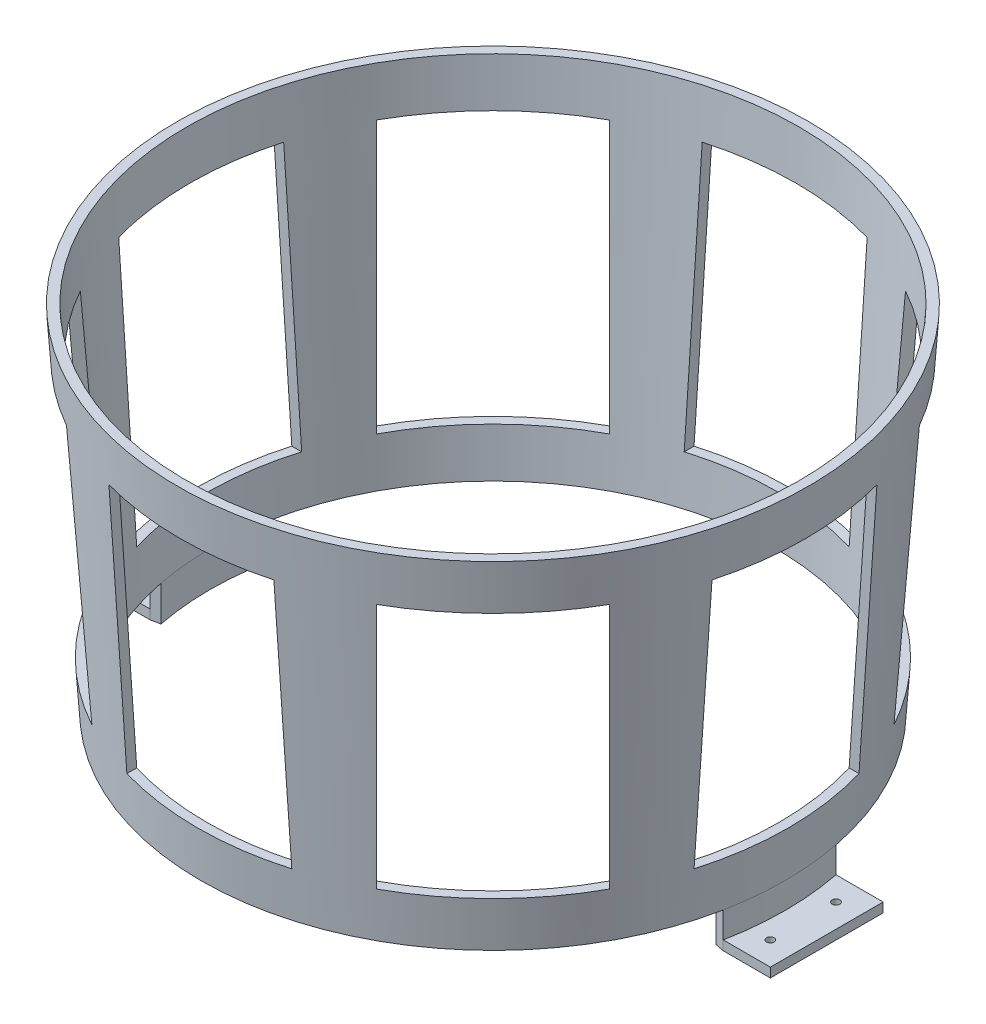
SolidWorks part; units mm, degrees
ref_plane "Front Plane" through (0, 0, 0) normal (0, 0, 1) x (1, 0, 0)
ref_plane "Top Plane" through (0, 0, 0) normal (0, 1, 0) x (1, 0, 0)
ref_plane "Right Plane" through (0, 0, 0) normal (1, 0, 0) x (0, 0, -1)
sketch "Sketch2" plane through (0, 0, 0) normal (0, 0, 1) x (1, 0, 0)
  line L1 (120, 0) -> (130, 150)
  line L2 (0, 0) -> (0, 173.8578) construction
  line L7 (120, 0) -> (124.0089, 0)
  line L8 (0, 0) -> (134.0323, 0) construction
  line L9 (130, 150) -> (134.0089, 150)
  line L10 (134.0089, 150) -> (124.0089, 0)
  dimension "D1" = 120
  dimension "D2" = 130
  dimension "D3" = 4
  dimension "D4" = 150
  dimension "D5" = 4
  dimension "D6" = 4.0089
revolve "Revolve1" add sketch "Sketch2" angle 360 about L2
sketch "Sketch4" [suppressed] plane through (0, 0, 0) normal (0, 0, 1) x (1, 0, 0)
  line L0 (0, 0) -> (0, 150) construction
  line L1 (-124.0089, 0) -> (124.0089, 0) construction
  line L2 (130, 150) -> (-130, 150) construction
  line L3 (110, 25) -> (110, 125)
  line L4 (-20, 25) -> (-50, 25)
  line L5 (-20, 25) -> (-20, 125)
  line L6 (-20, 125) -> (-50, 125)
  line L7 (-50, 25) -> (-50, 125)
  line L8 (-70, 25) -> (-110, 25)
  line L9 (-70, 25) -> (-70, 125)
  line L10 (-70, 125) -> (-110, 125)
  line L11 (-110, 25) -> (-110, 125)
  line L12 (70, 25) -> (70, 125)
  line L13 (70, 25) -> (110, 25)
  line L14 (20, 25) -> (50, 25)
  line L15 (20, 25) -> (20, 125)
  line L16 (50, 25) -> (50, 125)
  line L17 (20, 125) -> (50, 125)
  line L18 (70, 125) -> (110, 125)
  dimension "D1" = 40
  dimension "D2" = 30
  dimension "D3" = 20
  dimension "D4" = 20
  dimension "D5" = 25
  dimension "D6" = 25
  dimension "D7" = 25
  dimension "D8" = 25
ref_plane "Plane2" through (0, 0, 134) normal (0, 0, 1) x (1, 0, 0)
sketch "Sketch6" plane through (0, 0, 134) normal (0, 0, 1) x (1, 0, 0)
  line L0 (0, 0) -> (0, 150) construction
  line L1 (134.0089, 150) -> (-134.0089, 150) construction
  line L3 (-35, 130) -> (35, 130)
  line L4 (-35, 130) -> (-35, 20)
  line L5 (-35, 20) -> (35, 20)
  line L6 (35, 130) -> (35, 20)
  dimension "D1" = 70
  dimension "D2" = 20
  dimension "D3" = 20
extrude "Cut-Extrude2" cut sketch "Sketch6" against normal mid plane 40
sketch "Sketch7" plane through (0, 0, 0) normal (0, 1, 0) x (1, 0, 0)
  line L0 (-117.7443, 23.1577) -> (-121.6778, 23.9314)
  line L2 (-117.7443, -23.1577) -> (-121.6778, -23.9314)
  line L3 (117.7443, -23.1577) -> (121.6778, -23.9314)
  line L4 (117.7443, 23.1577) -> (121.6778, 23.9314)
  circle A0 centre (0, 0) radius 120 construction
  circle A1 centre (0, 0) radius 124.0089 construction
  arc A2 (117.7443, -23.1577) -> (117.7443, 23.1577) centre (0, 0) ccw
  arc A3 (121.6778, -23.9314) -> (121.6778, 23.9314) centre (0, 0) ccw
  arc A5 (-117.7443, 23.1577) -> (-117.7443, -23.1577) centre (0, 0) ccw
  arc A6 (-121.6778, 23.9314) -> (-121.6778, -23.9314) centre (0, 0) ccw
extrude "Boss-Extrude1" add sketch "Sketch7" against normal blind 15
sketch "Sketch8" plane through (0, -15, 0) normal (0, -1, 0) x (1, 0, 0)
  line L0 (121.6778, 23.9314) -> (141.6778, 23.9314)
  line L1 (121.6778, -23.9314) -> (141.6778, -23.9314)
  line L2 (141.6778, -23.9314) -> (141.6778, 23.9314)
  line L3 (-121.6778, 23.9314) -> (-141.6778, 23.9314)
  line L4 (-121.6778, -23.9314) -> (-141.6778, -23.9314)
  line L5 (-141.6778, -23.9314) -> (-141.6778, 23.9314)
  arc A0 (-121.6778, 23.9314) -> (-121.6778, -23.9314) centre (0, 0) ccw construction
  arc A1 (-121.6778, 23.9314) -> (-121.6778, -23.9314) centre (0, 0) ccw
  arc A2 (121.6778, -23.9314) -> (121.6778, 23.9314) centre (0, 0) ccw construction
  arc A3 (121.6778, -23.9314) -> (121.6778, 23.9314) centre (0, 0) ccw
  dimension "D1" = 20
  dimension "D2" = 20
  dimension "D3" = 47.8627
  dimension "D4" = 20
  dimension "D5" = 20
extrude "Boss-Extrude2" add sketch "Sketch8" against normal blind 4
sketch "Sketch9" plane through (0, -15, 0) normal (0, -1, 0) x (1, 0, 0)
  line L0 (141.6778, 23.9314) -> (121.6778, 23.9314) construction
  line L1 (121.6778, -23.9314) -> (141.6778, -23.9314) construction
  line L2 (141.6778, -23.9314) -> (141.6778, 23.9314) construction
  line L3 (0, -90.75) -> (0, 90.75) construction
  circle A0 centre (131.6778, 13.9314) radius 1.6
  circle A1 centre (131.6778, -13.9314) radius 1.6
  circle A2 centre (-131.6778, -13.9314) radius 1.6
  circle A3 centre (-131.6778, 13.9314) radius 1.6
  dimension "D1" = 3.2
  dimension "D2" = 3.2
  dimension "D3" = 10
  dimension "D4" = 10
  dimension "D5" = 10
  dimension "D6" = 10
extrude "Cut-Extrude3" cut sketch "Sketch9" against normal blind 24
pattern_circular "CirPattern1" count 8 over 360 about axis through (0, 0, 0) along (0, 1, 0) of "Cut-Extrude2"
ref_plane "Plane3" through (0, 130, 0) normal (0, -1, 0) x (-1, 0, 0)
